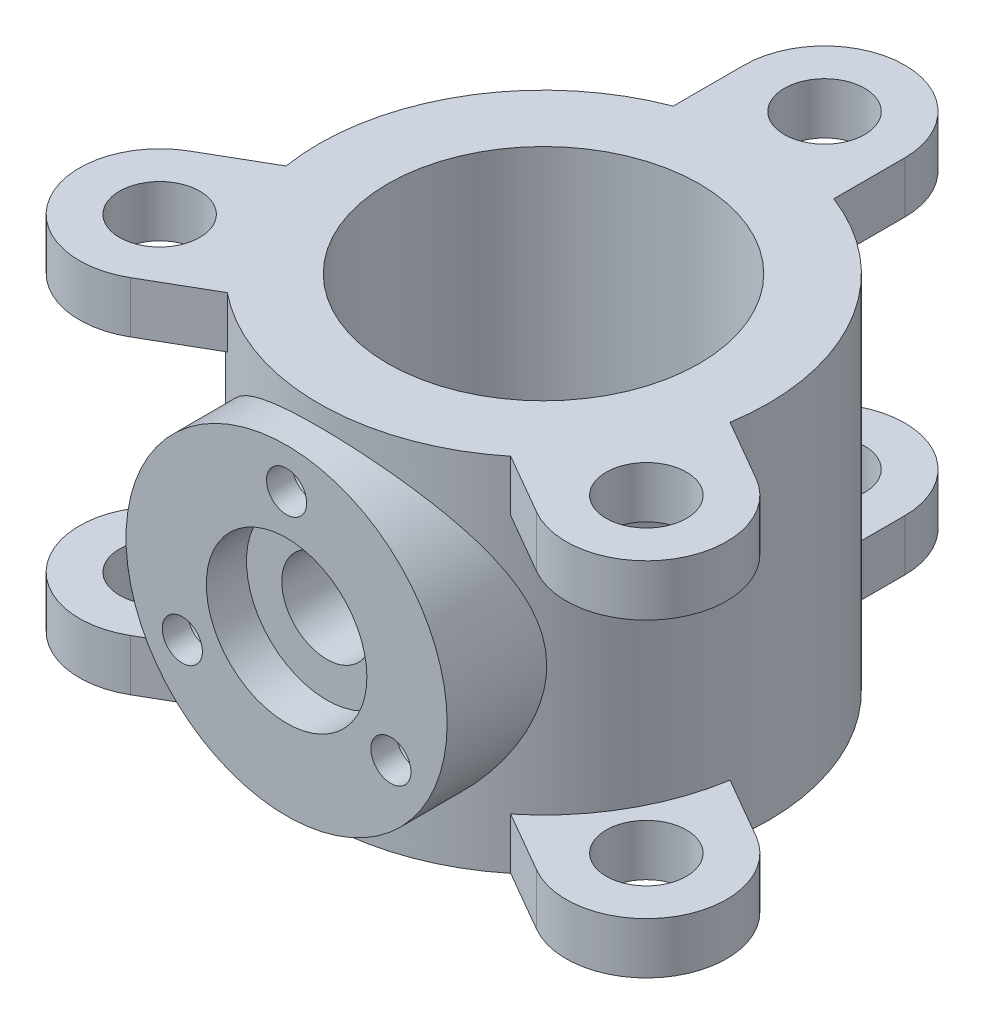
SolidWorks part; units mm, degrees
material "AISI 304"
ref_plane "Front Plane" through (0, 0, 0) normal (0, 0, 1) x (1, 0, 0)
ref_plane "Top Plane" through (0, 0, 0) normal (0, 1, 0) x (1, 0, 0)
ref_plane "Right Plane" through (0, 0, 0) normal (1, 0, 0) x (0, 0, -1)
sketch "Sketch1" plane through (0, 0, 0) normal (0, 1, 0) x (1, 0, 0)
  circle A0 centre (0, 0) radius 97
  circle A1 centre (0, 0) radius 140
  dimension "D1" = 280
  dimension "D2" = 194
extrude "Boss-Extrude1" add sketch "Sketch1" along normal mid plane 225
sketch "Sketch2" plane through (0, 112.5, 0) normal (0, 1, 0) x (1, 0, 0)
  line L2 (-50, 175) -> (-50, 130.767)
  line L3 (50, 175) -> (50, 130.767)
  circle A1 centre (0, 0) radius 140 construction
  arc A4 (50, 175) -> (-50, 175) centre (0, 175) ccw
  circle A6 centre (0, 175) radius 25
  arc A7 (50, 130.767) -> (-50, 130.767) centre (0, 0) ccw
  dimension "D4" = 50
  dimension "D6" = 50
  dimension "D5" = 175
extrude "Boss-Extrude2" add sketch "Sketch2" against normal blind 32
pattern_circular "CirPattern1" count 3 over 360 about axis through (0, 0, 0) along (0, 1, 0) of "Boss-Extrude2"
mirror "Mirror1" about plane through (0, 0, 0) normal (0, 1, 0) of "CirPattern1", "Boss-Extrude2"
ref_plane "Plane2" through (0, 0, 160) normal (0, 0, 1) x (1, 0, 0)
sketch "Sketch3" plane through (0, 0, 160) normal (0, 0, 1) x (1, 0, 0)
  circle A0 centre (0, 0) radius 100
  dimension "D1" = 200
extrude "Boss-Extrude3" add sketch "Sketch3" against normal up to next
sketch "Sketch4" plane through (0, 0, 160) normal (0, 0, 1) x (1, 0, 0)
  circle A0 centre (0, 0) radius 28
  dimension "D1" = 56
extrude "Cut-Extrude1" cut sketch "Sketch4" against normal up to next
sketch "Sketch5" plane through (0, 0, 160) normal (0, 0, 1) x (1, 0, 0)
  circle A0 centre (0, 0) radius 50
  dimension "D1" = 100
extrude "Cut-Extrude2" cut sketch "Sketch5" against normal blind 25
hole_wizard "Ø25.0mm Dowel Hole1" positions "Sketch6" profile "Sketch7" hole size "Ø25.0" standard "ANSI Metric"
sketch "Sketch6" plane through (0, 0, 160) normal (0, 0, 1) x (1, 0, 0)
  point P0 (0, 75)
  dimension "D1" = 75
sketch "Sketch7" plane through (0, 75, 160) normal (1, 0, 0) x (0, -1, 0)
  line L0 (0, 0) -> (0, 23.5108)
  line L1 (0, 23.5108) -> (12.5, 16)
  line L2 (12.5, 16) -> (12.5, 0)
  line L5 (12.5, 0) -> (0, 0)
  line L10 (0, 23.5108) -> (-12.5, 16) construction
  line L11 (0, -6.35) -> (0, 107.95) construction
  dimension "Hole Dia." = 25
  dimension "Hole Depth" = 16
  dimension "Drill Angle" = 118
pattern_circular "CirPattern2" count 3 over 360 about axis through (0, 0, 0) along (0, 0, 1) of "Ø25.0mm Dowel Hole1"
